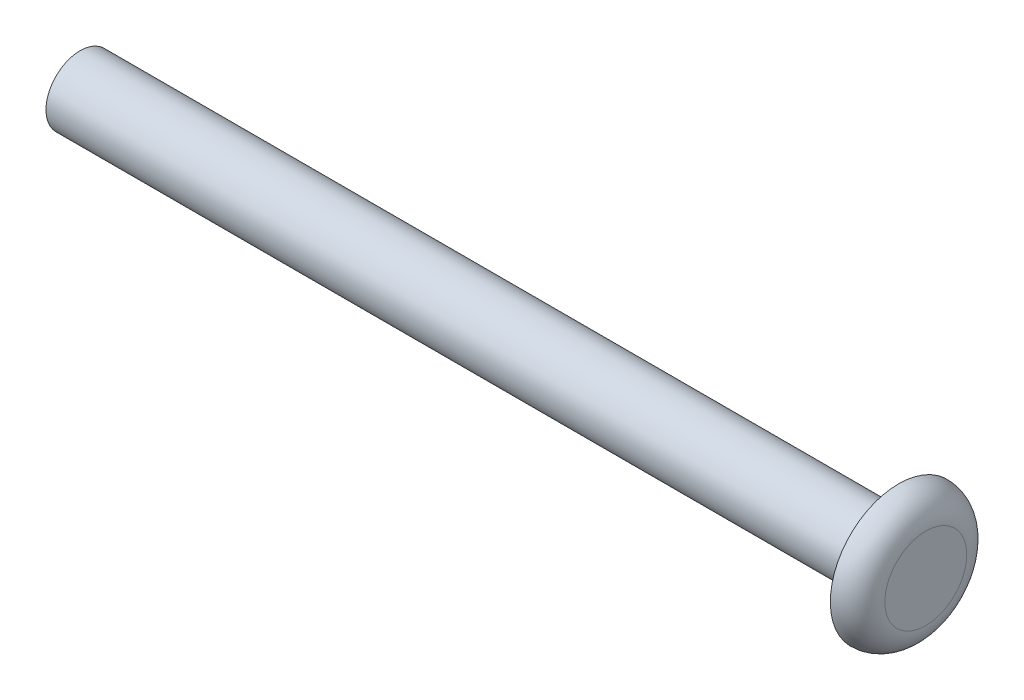
SolidWorks part; units mm, degrees
ref_plane "Front Plane" through (0, 0, 0) normal (0, 0, 1) x (1, 0, 0)
ref_plane "Top Plane" through (0, 0, 0) normal (0, 1, 0) x (1, 0, 0)
ref_plane "Right Plane" through (0, 0, 0) normal (1, 0, 0) x (0, 0, -1)
sketch "Sketch1" plane through (0, 0, 0) normal (0, 0, 1) x (1, 0, 0)
  line L0 (0, 0) -> (-78.74, 0)
  line L1 (-78.74, 0) -> (-78.74, 3.175)
  line L2 (-78.74, 3.175) -> (-2.54, 3.175)
  line L3 (-2.54, 3.175) -> (-2.54, 6.35)
  line L4 (0, 3.81) -> (0, 0)
  arc A0 (-2.54, 6.35) -> (0, 3.81) centre (-2.54, 3.81) cw
  dimension "D1" = 2.54
  dimension "D2" = 3.175
  dimension "D3" = 6.35
  dimension "D4" = 76.2
revolve "Revolve1" add sketch "Sketch1" angle 360 about L0
